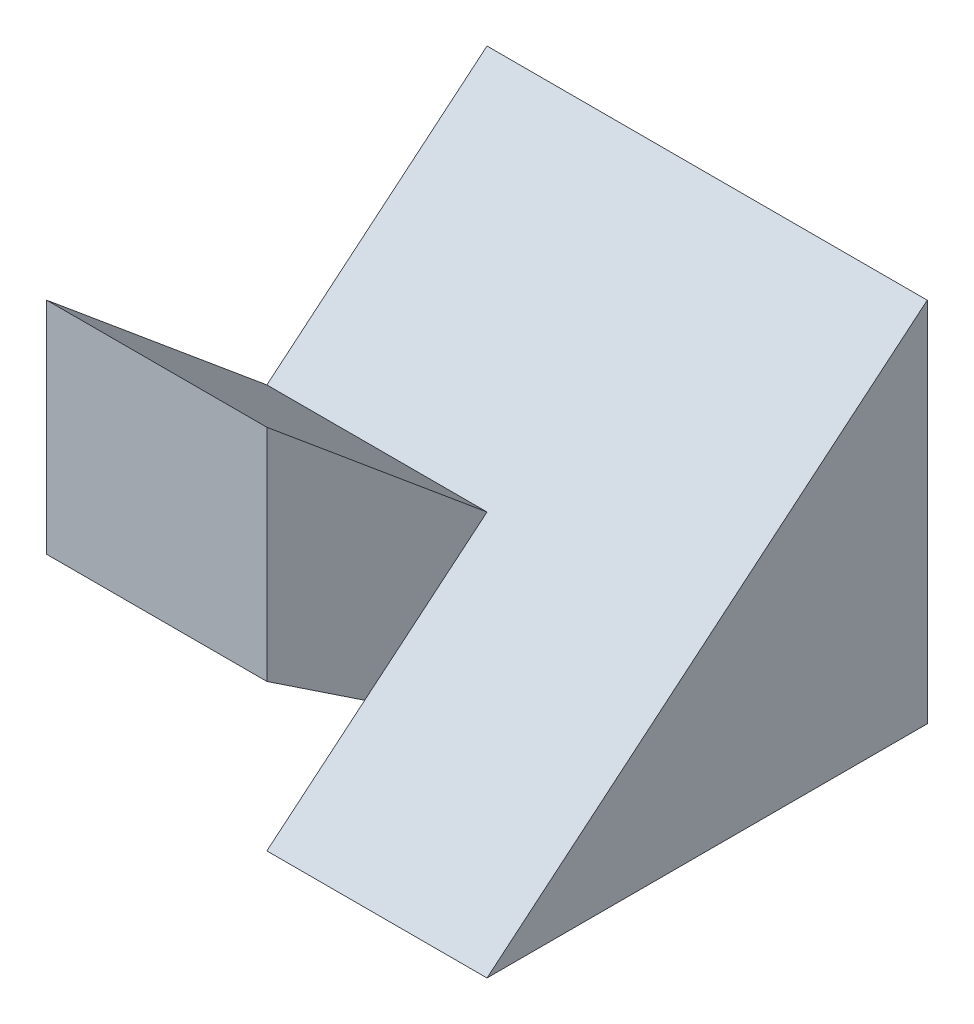
SolidWorks part; units mm, degrees
ref_plane "Front" through (0, 0, 0) normal (0, 0, 1) x (1, 0, 0)
ref_plane "Top" through (0, 0, 0) normal (0, 1, 0) x (1, 0, 0)
ref_plane "Right" through (0, 0, 0) normal (1, 0, 0) x (0, 0, -1)
sketch "Sketch1" plane through (0, 0, 0) normal (0, 1, 0) x (1, 0, 0)
  line L1 (-3, -3) -> (3, -3)
  line L2 (-3, -3) -> (-3, 3)
  line L3 (-3, 3) -> (3, 3)
  line L4 (3, -3) -> (3, 3)
  line L5 (-3, -3) -> (3, 3) construction
  line L6 (-3, 3) -> (3, -3) construction
  point P0 (0, 0)
  dimension "D1" = 6
  dimension "D2" = 6
extrude "Boss-Extrude1" add sketch "Sketch1" along normal blind 5
sketch "Sketch2" plane through (-3, 0, 0) normal (-1, 0, 0) x (0, 0, 1)
  line L0 (-3, 5) -> (0, 2.5)
  line L2 (0, 2.5) -> (3, 5)
  line L4 (-3, 0) -> (3, 0)
  line L5 (3, 0) -> (3, 5)
  line L6 (3, 5) -> (-3, 5)
  line L7 (-3, 5) -> (-3, 0)
  line L8 (-3, 0) -> (3, 0)
  line L9 (3, 0) -> (3, 5)
  line L10 (3, 5) -> (-3, 5)
  line L11 (-3, 5) -> (-3, 0)
  dimension "D1" = 0
extrude "Cut-Extrude1" cut sketch "Sketch2" against normal blind 10
sketch "Sketch3" plane through (3, 0, 0) normal (1, 0, 0) x (0, 0, -1)
  line L0 (3, 5) -> (-3, 0)
  line L6 (3, 5) -> (0, 2.5)
  line L7 (3, 5) -> (0, 2.5)
  line L8 (-3, 5) -> (-3, 0)
  line L9 (-3, 0) -> (3, 0)
  line L10 (3, 0) -> (3, 5)
  line L11 (0, 2.5) -> (-3, 5)
  line L12 (0, 2.5) -> (-3, 5)
  line L13 (-3, 5) -> (-3, 0)
  line L14 (-3, 0) -> (3, 0)
  line L15 (3, 0) -> (3, 5)
  dimension "D1" = 0
extrude "Cut-Extrude2" cut sketch "Sketch3" against normal blind 3
sketch "Sketch4" plane through (-3, 0, 0) normal (-1, 0, 0) x (0, 0, 1)
  line L0 (3, 5) -> (3, 0) construction
  line L1 (0, 0) -> (3, 0)
  line L4 (3, 0) -> (3, 2)
  line L5 (0, 0) -> (3, 2)
  dimension "D1" = 2
extrude "Cut-Extrude3" cut sketch "Sketch4" against normal blind 3
